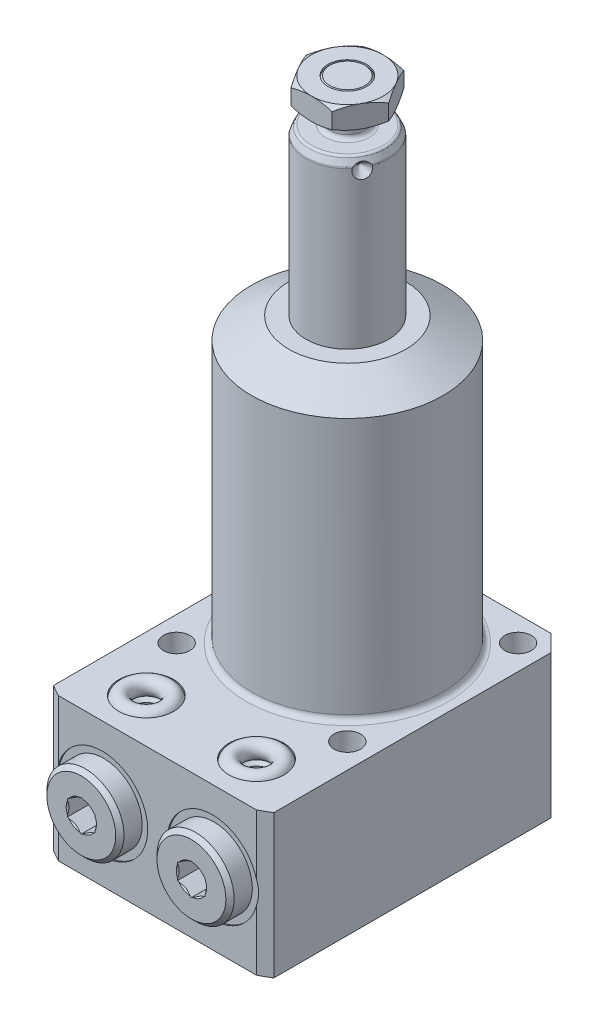
SolidWorks part; units mm, degrees
material "Alloy Steel"
ref_plane "Front Plane" through (0, 0, 0) normal (0, 0, 1) x (1, 0, 0)
ref_plane "Top Plane" through (0, 0, 0) normal (0, 1, 0) x (1, 0, 0)
ref_plane "Right Plane" through (0, 0, 0) normal (1, 0, 0) x (0, 0, -1)
sketch "Sketch1" plane through (0, 0, 0) normal (0, 0, 1) x (1, 0, 0)
  line L0 (7.5, 0) -> (7.5, 80)
  line L1 (7.5, 80) -> (6.8005, 81.5)
  line L2 (6.8005, 81.5) -> (3.25, 81.5)
  line L3 (3.25, 81.5) -> (3.25, 83.5)
  line L4 (3.25, 83.5) -> (3.935, 84.185)
  line L5 (3.935, 84.185) -> (3.935, 88.5)
  line L6 (3.935, 88.5) -> (3.185, 89.25)
  line L7 (3.185, 89.25) -> (0, 89.25)
  line L8 (0, -3.075) -> (0, 64.575) construction
  line L9 (7.5, 0) -> (0, 0)
  line L10 (0, 0) -> (0, 89.25)
  line L11 (-25.0821, -26) -> (21.8096, -26) construction
  dimension "D1" = 7.75
  dimension "D2" = 15
  dimension "D3" = 6.5
  dimension "D4" = 7.87
  dimension "D5" = 26
  dimension "D6" = 25
  dimension "D7" = 1.5
  dimension "D8" = 45
  dimension "D9" = 0.75
  dimension "D10" = 5.065
  dimension "D11" = 115.25
revolve "Revolve2" add sketch "Sketch1" angle 360 about L8
fillet "Fillet2" radius 0.75 2 edges at (0, 81.5, -3.25) (0, 83.5, -3.25)
fillet "Fillet3" radius 0.5 2 edges at (0, 80, -7.5) (0, 81.5, -6.8005)
sketch "Sketch2" plane through (0, 0, 0) normal (1, 0, 0) x (0, 0, -1)
  line L0 (6, 79.5) -> (7.5, 78)
  line L1 (4.2016, 79.5) -> (7.575, 79.5) construction
  line L2 (6.482, 81.5) -> (-6.482, 81.5) construction
  line L3 (7.5, 78) -> (7.5, 79.5)
  line L4 (7.5, 79.5) -> (6, 79.5)
  line L5 (7.5, 0) -> (7.5, 79.8892) construction
  dimension "D1" = 2
  dimension "D2" = 45
  dimension "D3" = 3
revolve "Cut-Revolve1" cut sketch "Sketch2" angle 360 about L1
sketch "Sketch3" plane through (0, 89.25, 0) normal (0, 1, 0) x (1, 0, 0)
  line L1 (7.5056, 0) -> (3.7528, 6.5)
  line L2 (3.7528, 6.5) -> (-3.7528, 6.5)
  line L3 (-3.7528, 6.5) -> (-7.5056, 0)
  line L4 (-7.5056, 0) -> (-3.7528, -6.5)
  line L5 (-3.7528, -6.5) -> (3.7528, -6.5)
  line L6 (3.7528, -6.5) -> (7.5056, 0)
  circle A0 centre (0, 0) radius 6.5 construction
  circle A1 centre (0, 0) radius 3.5
  dimension "D2" = 7
  dimension "D1" = 13
extrude "Extrude3" add sketch "Sketch3" against normal blind 4
pattern_circular "CirPattern1" count 3 over 360 about axis through (0, -3.075, 0) along (0, -1, 0) of "Cut-Revolve1"
sketch "Sketch4" plane through (0, 0, 0) normal (1, 0, 0) x (0, 0, -1)
  line L0 (6.5, 89.25) -> (9.5, 89.25)
  line L1 (9.5, 89.25) -> (9.5, 87.5179)
  line L2 (9.5, 87.5179) -> (6.5, 89.25)
  line L3 (6.5, 87.25) -> (-10.9636, 87.25) construction
  line L4 (6.5, 85.25) -> (6.5, 89.25) construction
  line L5 (9.5, 86.9821) -> (6.5, 85.25)
  line L6 (9.5, 85.25) -> (9.5, 86.9821)
  line L7 (6.5, 85.25) -> (9.5, 85.25)
  dimension "D1" = 30
  dimension "D2" = 3
revolve "Cut-Revolve3" cut sketch "Sketch4" angle 360 about axis through (0, -3.075, 0) along (0, -1, 0)
sketch "Sketch6" plane through (0, 0, 0) normal (0, 0, 1) x (1, 0, 0)
  line L0 (0, -26) -> (0, 67.6291) construction
  line L1 (0, 51.5) -> (10.625, 51.5)
  line L2 (10.625, 51.5) -> (17.385, 47.5971)
  line L3 (38.895, 0) -> (38.895, -26)
  line L4 (0, -26) -> (38.895, -26)
  line L5 (17.385, 0) -> (17.385, 47.5971)
  line L6 (38.895, 0) -> (17.385, 0)
  line L7 (0, -26) -> (0, 51.5)
  dimension "D1" = 34.77
  dimension "D2" = 26
  dimension "D3" = 77.5
  dimension "D4" = 77.79
  dimension "D5" = 30
  dimension "D6" = 21.25
revolve "Revolve3" add sketch "Sketch6" angle 360 about L0
sketch "Sketch7" plane through (0, 0, 0) normal (0, 1, 0) x (-1, 0, 0)
  line L0 (0, 0) -> (0, -52.3237) construction
  line L1 (-20, 34.5) -> (20, 34.5)
  line L2 (-20, 34.5) -> (-20, -20)
  line L3 (-20, -20) -> (20, -20)
  line L4 (20, 34.5) -> (20, -20)
  dimension "D1" = 40
  dimension "D2" = 54.5
  dimension "D3" = 20
extrude "Cut-Extrude5" cut sketch "Sketch7" against normal through all flip side to cut
sketch "Sketch8" plane through (0, -26, 0) normal (0, -1, 0) x (1, 0, 0)
  circle A0 centre (-15.5, 15.5) radius 2.4
  dimension "D1" = 4.8
  dimension "D2" = 15.5
  dimension "D3" = 15.5
extrude "Cut-Extrude6" cut sketch "Sketch8" against normal through all
pattern_circular "CirPattern2" count 4 over 360 about axis through (0, 0, 0) along (0, 1, 0) of "Cut-Extrude6"
chamfer "Chamfer1" distance 3 angle 45 2 edges at (-20, -13, -20) (20, -13, -20)
fillet "Fillet5" radius 1 1 edges at (0, 0, -17.385)
ref_plane "Plane1" through (0, -13, 0) normal (0, -1, 0) x (1, 0, 0)
sketch "Sketch11" plane through (0, -13, 0) normal (0, -1, 0) x (1, 0, 0)
  line L0 (-10, 42.9716) -> (-10, 19.7499) construction
  line L1 (-18.25, 34.5) -> (-18.25, 34.25)
  line L3 (-18.25, 34.25) -> (-15, 34.25)
  line L4 (-15, 34.25) -> (-14.42, 33.67)
  line L5 (-14.42, 33.67) -> (-14.42, 19.09)
  line L6 (-14.42, 19.09) -> (-10, 19.09)
  line L7 (-10, 19.09) -> (-10, 34.5)
  line L8 (-10, 34.5) -> (-18.25, 34.5)
  line L10 (17.9603, 34.5) -> (-17.9603, 34.5) construction
  dimension "D1" = 10
  dimension "D2" = 0.25
  dimension "D3" = 8.84
  dimension "D4" = 15.16
  dimension "D5" = 16.5
  dimension "D6" = 45
  dimension "D7" = 0.58
revolve "Cut-Revolve5" cut sketch "Sketch11" angle 360 about L0
ref_plane "Plane2" through (0, 0, 26.5) normal (0, 0, 1) x (1, 0, 0)
sketch "Sketch13" plane through (0, 0, 26.5) normal (0, 0, 1) x (1, 0, 0)
  line L0 (-12.5, -14) -> (-12.5, -23.125)
  line L1 (-12.5, -23.125) -> (-13.125, -23.75)
  line L2 (-13.125, -23.75) -> (-15, -23.75)
  line L3 (-15, -23.75) -> (-15, -26)
  line L5 (-15, -26) -> (-10, -26)
  line L6 (-10, -26) -> (-10, -14)
  line L7 (-10, -14) -> (-12.5, -14)
  line L8 (-10, 15.2099) -> (-10, -4.3918) construction
  line L10 (17.9603, -26) -> (-17.9603, -26) construction
  dimension "D1" = 10
  dimension "D2" = 5
  dimension "D3" = 12
  dimension "D4" = 2.25
  dimension "D5" = 10
  dimension "D6" = 45
  dimension "D7" = 0.625
revolve "Cut-Revolve6" cut sketch "Sketch13" angle 360 about L8
sketch "Sketch14" plane through (0, -13, 0) normal (0, -1, 0) x (1, 0, 0)
  line L0 (-10, 32.5881) -> (-10, 43.3353) construction
  line L1 (-10, 19.09) -> (-10, 33.67) construction
  line L2 (-12.75, 38.31) -> (-16.25, 38.31)
  line L3 (-16.25, 38.31) -> (-17, 37.56)
  line L4 (-17, 37.56) -> (-17, 34.25)
  line L5 (-1.75, 34.25) -> (-18.25, 34.25) construction
  line L6 (-17, 34.25) -> (-14.125, 34.25)
  line L7 (-5, 34.25) -> (-15, 34.25) construction
  line L8 (-14.125, 34.25) -> (-14.125, 31.8078)
  line L9 (-14.125, 31.8078) -> (-10, 31.8078)
  line L10 (-10, 31.8078) -> (-10, 31.8088)
  line L11 (-10, 31.8088) -> (-12.5, 33.311)
  line L12 (-12.5, 33.311) -> (-12.5, 38.06)
  line L13 (-12.5, 38.06) -> (-12.75, 38.31)
  dimension "D1" = 8.25
  dimension "D2" = 2.4422
  dimension "D3" = 59
  dimension "D4" = 5
  dimension "D5" = 4.06
  dimension "D6" = 14
  dimension "D7" = 45
  dimension "D8" = 0.75
  dimension "D9" = 45
  dimension "D10" = 0.25
  dimension "D11" = 0.001
revolve "Revolve6" add sketch "Sketch14" angle 360 about L0
mirror "Mirror4" about plane through (0, -13, 0) normal (0, -1, 0) of "Cut-Revolve6"
sketch "Sketch15" plane through (0, 0, 38.31) normal (0, 0, 1) x (1, 0, 0)
  line L1 (-7.5, -14.4434) -> (-7.5, -11.5566)
  line L2 (-7.5, -11.5566) -> (-10, -10.1132)
  line L3 (-10, -10.1132) -> (-12.5, -11.5566)
  line L4 (-12.5, -11.5566) -> (-12.5, -14.4434)
  line L5 (-12.5, -14.4434) -> (-10, -15.8868)
  line L6 (-10, -15.8868) -> (-7.5, -14.4434)
  circle A0 centre (-10, -13) radius 2.5 construction
  dimension "D1" = 5
extrude "Cut-Extrude8" cut sketch "Sketch15" against normal blind 4.06
mirror "Mirror1" about plane through (0, 0, 0) normal (1, 0, 0) of "Mirror4", "Cut-Revolve5", "Cut-Revolve6", "Revolve6", "Cut-Extrude8"
sketch "Sketch16" plane through (0, 0, 26.5) normal (0, 0, 1) x (1, 0, 0)
  line L1 (-10, 9.3219) -> (-10, -15.1063) construction
  line L2 (-10, -23.125) -> (-10, -16.6451) construction
  line L3 (17.9603, -26) -> (-17.9603, -26) construction
  circle A0 centre (-13.5, -25.25) radius 1.5
  dimension "D1" = 3
  dimension "D3" = 0.75
  dimension "D2" = 7
revolve "Revolve7" add sketch "Sketch16" angle 360 about L1
mirror "Mirror3" about plane through (0, 0, 0) normal (1, 0, 0) of bodies 128
mirror "Mirror5" about plane through (0, -13, 0) normal (0, -1, 0) of bodies 128 130
